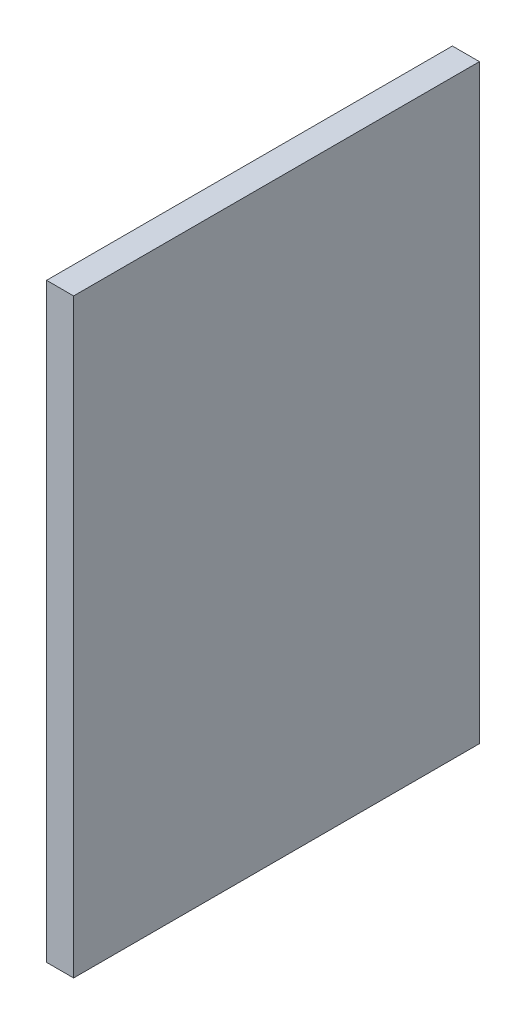
SolidWorks part; units mm, degrees
ref_plane "Front Plane" through (0, 0, 0) normal (0, 0, 1) x (1, 0, 0)
ref_plane "Top Plane" through (0, 0, 0) normal (0, 1, 0) x (1, 0, 0)
ref_plane "Right Plane" through (0, 0, 0) normal (1, 0, 0) x (0, 0, -1)
sketch "Sketch4" plane through (0, 0, 0) normal (0, 0, 1) x (1, 0, 0)
  line L0 (0, 0) -> (36.6665, 419.1) construction
  line L1 (36.6665, 419.1) -> (155.7226, 419.1) construction
  line L2 (155.7226, 419.1) -> (155.7226, 0) construction
  line L3 (155.7226, 0) -> (0, 0) construction
  line L4 (155.7226, -1000) -> (155.7226, 49000) construction
  line L5 (1.8042, 20.6221) -> (36.6665, 419.1) construction
  line L6 (1.8042, 20.6221) -> (41.652, 17.1359) construction
  line L7 (36.6665, 419.1) -> (76.5143, 415.6138) construction
  line L8 (41.652, 17.1359) -> (76.5143, 415.6138) construction
  line L9 (60.4726, -1000) -> (60.4726, 49000) construction
  line L10 (-52.7184, 317.5) -> (-128.6284, 324.1413) construction
  line L11 (-30.1965, 414.3375) -> (36.6601, 414.3375) construction
  line L12 (-1162.1335, 304.8) -> (48837.8665, 304.8) construction
  line L13 (-130.0274, 292.1) -> (-53.8274, 292.1) construction
  line L14 (-128.6284, 324.1413) -> (-53.8274, 292.1) construction
  line L15 (-52.7184, 317.5) -> (-130.0274, 292.1) construction
  line L16 (36.6601, 338.1375) -> (-30.1965, 338.1375) construction
  line L17 (-138.1172, 324.9714) -> (27.1662, 310.511)
  line L18 (-138.1172, 324.9714) -> (-137.5638, 331.2973)
  line L19 (-137.5638, 331.2973) -> (36.6665, 419.1)
  line L20 (36.6665, 419.1) -> (104.9226, 419.1)
  line L21 (104.9226, 419.1) -> (104.9226, 0) construction
  line L22 (27.1662, 310.511) -> (0.3389, 3.8741)
  line L23 (0.3389, 3.8741) -> (44.6198, 0)
  line L24 (44.6198, 0) -> (104.9226, 0)
  line L25 (104.9226, 419.1) -> (155.7226, 311.15)
  line L26 (155.7226, 311.15) -> (155.7226, 304.8)
  line L27 (155.7226, 304.8) -> (104.9226, 280.8941)
  line L28 (104.9226, 280.8941) -> (104.9226, 0)
  arc A0 (-128.6284, 324.1413) -> (-30.1965, 414.3375) centre (-30.1965, 315.5296) cw construction
  arc A1 (69.9976, 304.8) -> (36.6601, 338.1375) centre (36.6601, 304.8) ccw construction
  arc A2 (146.1976, 304.8) -> (36.6601, 414.3375) centre (36.6601, 304.8) ccw construction
  arc A3 (-52.7184, 317.5) -> (-30.1965, 338.1375) centre (-30.1965, 315.5296) cw construction
  point P7 (54.1226, 400.05)
  point P17 (146.1976, 304.8)
  point P18 (69.9976, 304.8)
  dimension "D9" = 9.525
  dimension "D14" = 25.4
  dimension "D1" = 419.1
  dimension "D2" = 101.6
  dimension "D3" = 19.05
  dimension "D4" = 19.05
  dimension "D5" = 85
  dimension "D6" = 40
  dimension "D7" = 400
  dimension "D8" = 95.25
  dimension "D10" = 9.525
  dimension "D11" = 114.3
  dimension "D12" = 76.2
  dimension "D13" = 9.525
  dimension "D15" = 127
  dimension "D16" = 9.525
  dimension "D17" = 209.55
  dimension "D18" = 6.35
  dimension "D19" = 50.8
  dimension "D20" = 44.45
  dimension "D21" = 6.35
sketch "Sketch5" plane through (0, 0, 0) normal (0, 0, 1) x (1, 0, 0)
  line L0 (60.4726, -201000) -> (60.4726, 249000) construction
  line L1 (60.4726, 311.15) -> (54.1226, 311.15)
  line L2 (60.4726, 311.15) -> (60.4726, 172.5114)
  line L3 (60.4726, 172.5114) -> (54.1226, 172.5114)
  line L4 (54.1226, 311.15) -> (54.1226, 172.5114)
  line L5 (-201162.1335, 304.8) -> (248837.8665, 304.8) construction
  line L6 (40.2644, -52.6511) -> (4398.0515, 49757.0838) construction
  line L7 (27.1662, 310.511) -> (0.3389, 3.8741) construction
  line L8 (60.4726, 178.3301) -> (55.7905, 178.7397) construction
  line L9 (41.652, 17.1359) -> (76.5143, 415.6138) construction
  point P12 (60.4726, 178.3301)
  dimension "D1" = 6.35
  dimension "D2" = 44.7
  dimension "D3" = 6.35
  dimension "D4" = 6.35
extrude "Boss-Extrude1" add sketch "Sketch5" along normal blind 95.25
